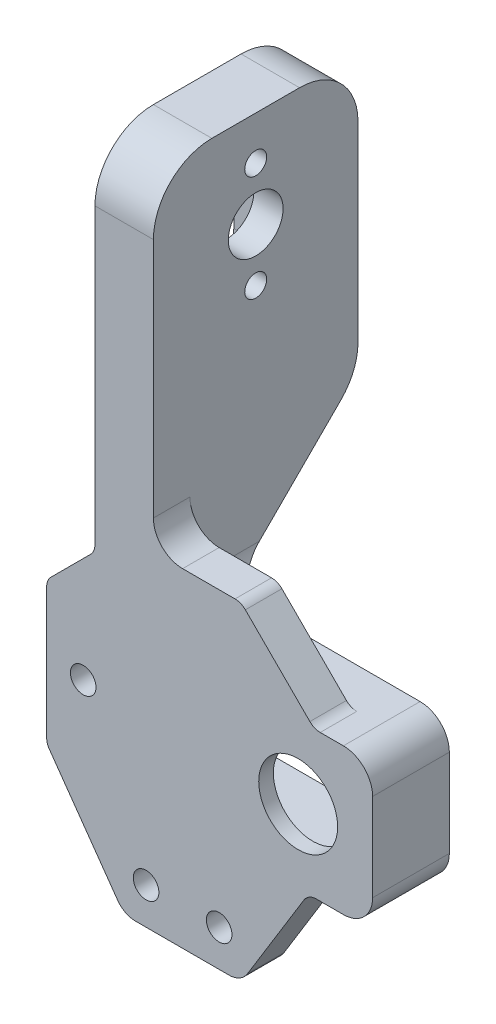
SolidWorks part; units mm, degrees
ref_plane "Ön Düzlem" through (0, 0, 0) normal (0, 0, 1) x (1, 0, 0)
ref_plane "Üst Düzlem" through (0, 0, 0) normal (0, 1, 0) x (1, 0, 0)
ref_plane "Sağ Düzlem" through (0, 0, 0) normal (1, 0, 0) x (0, 0, -1)
sketch "Çizim1" plane through (0, 0, 0) normal (0, 0, 1) x (1, 0, 0)
  line L0 (-4, 32.6972) -> (4, 32.6972)
  line L1 (4, 32.6972) -> (4, -8.3028)
  line L2 (-0.8966, -56.0348) -> (0, -57.3028)
  line L3 (-4, -12.3028) -> (-4, 32.6972)
  line L4 (0, -49.5) -> (0, 49.5) construction
  line L5 (-4.5858, -16.8886) -> (-10.0208, -22.3236)
  line L6 (-4, -12.3028) -> (-4, -15.4744)
  line L7 (-10.6066, -23.7378) -> (-10.6066, -41.6671)
  line L8 (-0.8966, -56.0348) -> (-10.2396, -42.8218)
  line L9 (1.5529, -57.3028) -> (14.3204, -57.3028)
  line L10 (16.8779, -55.871) -> (24.6121, -43.2573)
  line L11 (8, -12.3028) -> (15.1716, -12.3028)
  line L12 (16.5858, -12.8886) -> (25.4142, -21.717)
  line L13 (26.8284, -22.3028) -> (30, -22.3028)
  line L14 (26.3172, -42.3028) -> (30, -42.3028)
  line L15 (34, -26.3028) -> (34, -38.3028)
  line L16 (15.1716, -12.3028) -> (16.1292, -12.3028)
  line L17 (16.5858, -12.8886) -> (15.1065, -11.4093)
  arc A0 (30, -22.3028) -> (34, -26.3028) centre (30, -26.3028) cw
  arc A1 (30, -42.3028) -> (34, -38.3028) centre (30, -38.3028) ccw
  arc A2 (4, -8.3028) -> (8, -12.3028) centre (8, -8.3028) ccw
  arc A3 (16.5858, -12.8886) -> (15.1716, -12.3028) centre (15.1716, -14.3028) ccw
  arc A4 (25.4142, -21.717) -> (26.8284, -22.3028) centre (26.8284, -20.3028) ccw
  arc A5 (26.3172, -42.3028) -> (24.6121, -43.2573) centre (26.3172, -44.3028) ccw
  arc A6 (1.5529, -57.3028) -> (-0.8966, -56.0348) centre (1.5529, -54.3028) cw
  arc A7 (14.3204, -57.3028) -> (16.8779, -55.871) centre (14.3204, -54.3028) ccw
  arc A8 (-4.5858, -16.8886) -> (-4, -15.4744) centre (-6, -15.4744) ccw
  arc A9 (-10.6066, -23.7378) -> (-10.0208, -22.3236) centre (-8.6066, -23.7378) cw
  arc A10 (-10.2396, -42.8218) -> (-10.6066, -41.6671) centre (-8.6066, -41.6671) cw
  circle A11 centre (3, -52.3028) radius 1.75
  circle A12 centre (13, -52.3028) radius 1.75
  circle A13 centre (-5.6066, -32.3028) radius 1.75
  circle A14 centre (23.8142, -32.3028) radius 5.4
  point P18 (34, -22.3028)
  point P21 (34, -42.3028)
  point P24 (4, -12.3028)
  point P27 (16, -12.3028)
  point P30 (26, -22.3028)
  point P33 (25.1974, -42.3028)
  point P36 (0, -57.3028)
  point P39 (16, -57.3028)
  point P46 (-10.6066, -42.3028)
  dimension "D4" = 4
  dimension "D6" = 4
  dimension "D9" = 4
  dimension "D14" = 2
  dimension "D15" = 2
  dimension "D16" = 2
  dimension "D17" = 3
  dimension "D18" = 2
  dimension "D21" = 3.5
  dimension "D22" = 3.5
  dimension "D20" = 3.5
  dimension "D1" = 8
  dimension "D2" = 4
  dimension "D3" = 45
  dimension "D5" = 15
  dimension "D7" = 16
  dimension "D8" = 15
  dimension "D10" = 10
  dimension "D11" = 10
  dimension "D12" = 18
  dimension "D13" = 18
  dimension "D23" = 10
  dimension "D24" = 10
extrude "Yükseklik-Ekstrüzyon1" add sketch "Çizim1" along normal blind 10.5 contours A10 L8 A6 L9 A7 L10 A5 L14 A1 L15 A0 L13 A4 L12 A3 L11 A2 L1 L0 L3 L6 A8 L5 A9 L7 A14 A13 A12 A11
ref_plane "Düzlem1" through (4, 0, 0) normal (1, 0, 0) x (0, 0, -1)
sketch "Çizim3" plane through (4, 0, 0) normal (1, 0, 0) x (0, 0, -1)
  line L0 (-5.5, -22.3028) -> (0, -22.3028)
  line L1 (0, 44.2089) -> (0, -44.2089) construction
  line L2 (-10.5, -22.3028) -> (0, -22.3028) construction
  line L3 (0, -22.3028) -> (0, -8.3028)
  line L4 (-10.5, -8.3028) -> (0, -8.3028) construction
  line L5 (0, -8.3028) -> (-5.5, -8.3028)
  line L6 (-5.5, -8.3028) -> (-5.5, -22.3028)
  dimension "D1" = 5.5
extrude "Kes-Ekstrüzyon1" cut sketch "Çizim3" along normal blind 34.5
sketch "Çizim4" plane through (0, 0, 0) normal (1, 0, 0) x (0, 0, -1)
  line L0 (-5.5, -42.8218) -> (-5.5, -42.3028)
  line L1 (-10.5, -57.3028) -> (0, -57.3028) construction
  line L4 (0, -57.3028) -> (-5.5, -57.3028)
  line L5 (-5.5, -57.3028) -> (-5.5, -42.8218)
  line L6 (0, -42.8218) -> (0, -57.3028)
  line L7 (0, 44.2089) -> (0, -44.2089) construction
  line L8 (-10.5, -42.3028) -> (0, -42.3028) construction
  line L9 (-5.5, -42.3028) -> (0, -42.3028)
  line L10 (0, -42.3028) -> (0, -42.8218)
extrude "Kes-Ekstrüzyon2" cut sketch "Çizim4" against normal blind 34.5 and the other way blind 34.5
sketch "Çizim5" plane through (0, 0, 0) normal (0, 1, 0) x (1, 0, 0)
  line L0 (-4, -5.5) -> (-4, 0)
  line L1 (-4, -10.5) -> (-4, 0) construction
  line L2 (-44.2089, 0) -> (44.2089, 0) construction
  line L3 (-4, 0) -> (-10.6066, 0)
  line L4 (-10.6066, -10.5) -> (-10.6066, 0) construction
  line L5 (-10.6066, 0) -> (-10.6066, -5.5)
  line L6 (-10.6066, -5.5) -> (-4, -5.5)
  dimension "D1" = 5.5
extrude "Kes-Ekstrüzyon4" cut sketch "Çizim5" against normal blind 50.5
sketch "Çizim7" plane through (0, 0, 0) normal (0, 0, 1) x (1, 0, 0)
  line L0 (-10.6066, -22.9094) -> (-12.808, -22.9094)
  line L2 (-12.808, -22.9094) -> (-12.8079, -22.8759)
  line L3 (-10.6066, -22.9094) -> (-0.6066, -22.9094)
  line L4 (-0.6066, -26.9094) -> (-0.6066, -37.3028)
  line L5 (4.3934, -42.3028) -> (4.3934, -45.4483)
  line L7 (26.3172, -42.3028) -> (-4, -42.3028) construction
  line L8 (4.3934, -45.4483) -> (-12.808, -45.4483)
  line L9 (-12.808, -45.4483) -> (-12.808, -22.9094)
  arc A0 (-0.6066, -26.9094) -> (-4.6066, -22.9094) centre (-4.6066, -26.9094) ccw
  arc A1 (-0.6066, -37.3028) -> (4.3934, -42.3028) centre (4.3934, -37.3028) ccw
  dimension "D1" = 10
  dimension "D2" = 4
  dimension "D3" = 4
  dimension "D5" = 5
extrude "Kes-Ekstrüzyon5" cut sketch "Çizim7" along normal blind 5.5 contours A1 L4 A0 L3 L0 L9 L8 L5
sketch "Çizim8" plane through (4, 0, 0) normal (1, 0, 0) x (0, 0, -1)
  line L0 (-10.5, 32.6972) -> (9.5, 32.6972)
  line L1 (0, -22.3028) -> (15.1569, -7.1459)
  line L2 (0, 44.2089) -> (0, -44.2089) construction
  line L3 (17.5, 24.6972) -> (17.5, -1.3363)
  line L4 (-10.5, 32.6972) -> (-10.5, -22.3028)
  line L5 (-10.5, -22.3028) -> (0, -22.3028)
  line L6 (17.5, -1.3363) -> (17.5, -1.4891)
  arc A0 (15.1569, -7.1459) -> (17.5, -1.4891) centre (9.5, -1.4891) ccw
  arc A1 (17.5, 24.6972) -> (9.5, 32.6972) centre (9.5, 24.6972) ccw
  point P11 (17.5, 32.6972)
  dimension "D2" = 8
  dimension "D3" = 8
  dimension "D1" = 28
extrude "Yükseklik-Ekstrüzyon2" add sketch "Çizim8" against normal blind 8
fillet "Radyus2" radius 8 1 edges at (0, 32.6972, 10.5)
fillet "Radyus7" radius 4 1 edges at (4, -22.3028, 2.75)
sketch "Çizim9" plane through (0, 0, 0) normal (0, 0, 1) x (1, 0, 0)
  line L0 (7, -25.8028) -> (30, -25.8028)
  line L2 (7, -25.8028) -> (7, -38.8028)
  line L3 (30, -25.8028) -> (30, -38.8028)
  line L4 (30, -38.8028) -> (7, -38.8028)
extrude "Kes-Ekstrüzyon6" cut sketch "Çizim9" along normal blind 8.5
sketch "Çizim10" plane through (0, 0, 0) normal (0, 0, 1) x (1, 0, 0)
  line L2 (7, -25.8028) -> (7, -38.8028) construction
  line L4 (30, -38.8028) -> (30, -25.8028) construction
  circle A0 centre (32, -32.3028) radius 1
  circle A1 centre (5, -32.3028) radius 1
  dimension "D1" = 2
  dimension "D2" = 2
  dimension "D3" = 2
  dimension "D4" = 2
extrude "Kes-Ekstrüzyon7" cut sketch "Çizim10" along normal blind 6
ref_plane "Düzlem3" through (-4, 0, 0) normal (-1, 0, 0) x (0, 0, 1)
sketch "Çizim11" plane through (-4, 0, 0) normal (-1, 0, 0) x (0, 0, 1)
  line L6 (-6.5, 14.1972) -> (-6.5, 23.1972)
  line L7 (-0.5, 23.1972) -> (-0.5, 14.1972)
  arc A3 (-0.5, 23.1972) -> (-6.5, 23.1972) centre (-3.5, 23.1972) ccw
  arc A4 (-6.5, 14.1972) -> (-0.5, 14.1972) centre (-3.5, 14.1972) ccw
  dimension "D8" = 6
  dimension "D9" = 6
  dimension "D7" = 9
extrude "Kes-Ekstrüzyon8" cut sketch "Çizim11" against normal blind 4
sketch "Çizim12" plane through (-4, 0, 0) normal (-1, 0, 0) x (0, 0, 1)
  circle A0 centre (-3.5, 23.1972) radius 1.3
  circle A1 centre (-3.5, 14.1972) radius 1.3
  circle A2 centre (-3.5, 18.6972) radius 2.5
  dimension "D1" = 2.6
  dimension "D2" = 2.6
  dimension "D3" = 5
extrude "Kes-Ekstrüzyon9" cut sketch "Çizim12" against normal blind 8
sketch "Çizim13" plane through (4, 0, 0) normal (1, 0, 0) x (0, 0, -1)
  line L0 (-4.1895, 27.8464) -> (11.2025, 28.2284)
  line L1 (11.2025, 28.2284) -> (11.6838, 8.8341)
  line L2 (11.6838, 8.8341) -> (-4.1895, 8.4402)
  line L3 (-4.1895, 8.4402) -> (-4.1895, 27.8464)
  circle A0 centre (3.5, 18.6972) radius 2.5
extrude "Yükseklik-Ekstrüzyon4" add sketch "Çizim13" against normal blind 8
sketch "Çizim14" plane through (4, 0, 0) normal (1, 0, 0) x (0, 0, -1)
  circle A0 centre (3.5, 19.5063) radius 3.75
  circle A1 centre (3.5, 12.2563) radius 1.5
  circle A2 centre (3.5, 26.7563) radius 1.5
  dimension "D1" = 7.5
  dimension "D3" = 3
  dimension "D2" = 7.25
  dimension "D5" = 7.25
extrude "Kes-Ekstrüzyon10" cut sketch "Çizim14" against normal blind 8
sketch "Çizim15" plane through (-4, 0, 0) normal (-1, 0, 0) x (0, 0, 1)
  line L0 (-8.5, 9.5063) -> (-8.5, 29.5063)
  line L1 (-8.5, 29.5063) -> (1.5, 29.5063)
  line L2 (1.5, 29.5063) -> (1.5, 9.5063)
  line L4 (-8.5, 9.5063) -> (1.5, 9.5063)
  circle A0 centre (-3.5, 19.5063) radius 3.75 construction
  circle A1 centre (-3.5, 26.7563) radius 1.5
  point P2 (0, 0)
  dimension "D1" = 5
  dimension "D3" = 10
extrude "Kes-Ekstrüzyon11" cut sketch "Çizim15" against normal blind 4
fillet "Radyus10" radius 3 1 edges at (-2, 29.5063, 1.5)
fillet "Radyus11" radius 3 1 edges at (-2, 9.5063, -8.5)
fillet "Radyus12" radius 3 1 edges at (-2, 29.5063, -8.5)
fillet "Radyus13" radius 3 1 edges at (-2, 9.5063, 1.5)
